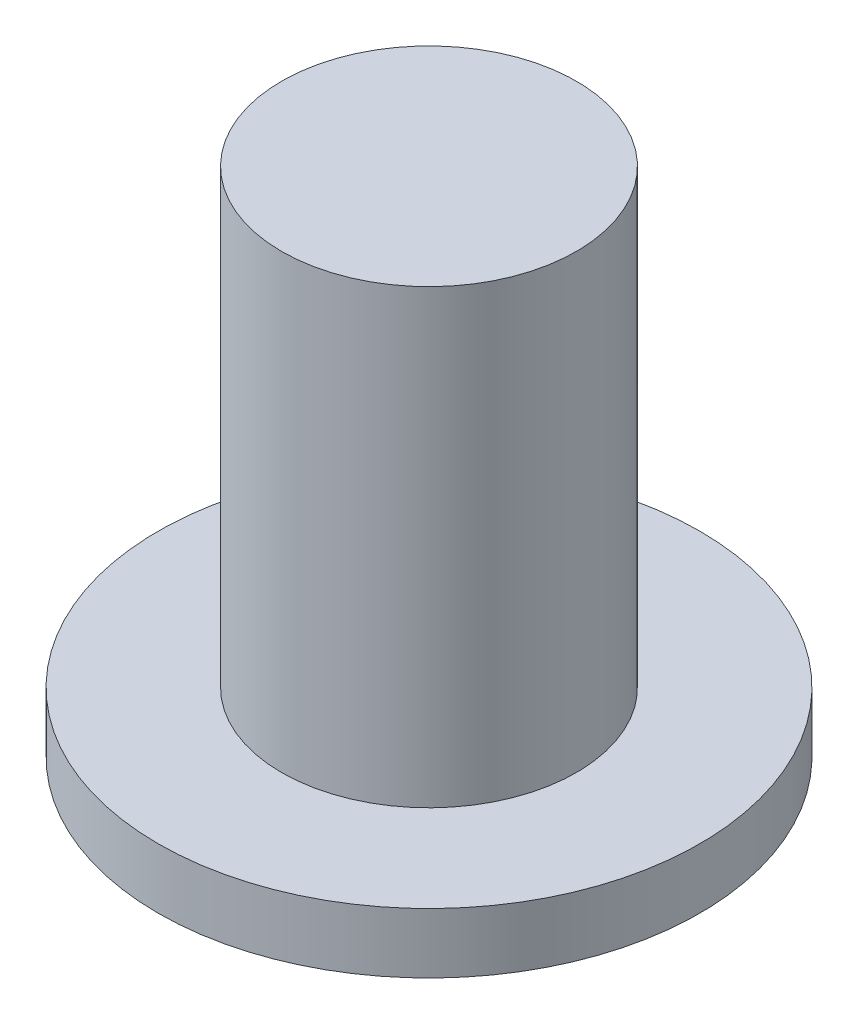
SolidWorks part; units mm, degrees
material "uhlíková ocel 7850"
ref_plane "Přední rovina" through (0, 0, 0) normal (0, 0, 1) x (1, 0, 0)
ref_plane "Horní rovina" through (0, 0, 0) normal (0, 1, 0) x (1, 0, 0)
ref_plane "Pravá rovina" through (0, 0, 0) normal (1, 0, 0) x (0, 0, -1)
sketch "Skica1" plane through (0, 0, 0) normal (0, 1, 0) x (1, 0, 0)
  circle A0 centre (0, 0) radius 9
  dimension "D1" = 18
extrude "Přidat vysunutím1" add sketch "Skica1" along normal blind 2
sketch "Skica2" plane through (0, 2, 0) normal (0, 1, 0) x (1, 0, 0)
  circle A0 centre (0, 0) radius 4.9
  dimension "D1" = 9.8
extrude "Přidat vysunutím2" add sketch "Skica2" along normal blind 15
